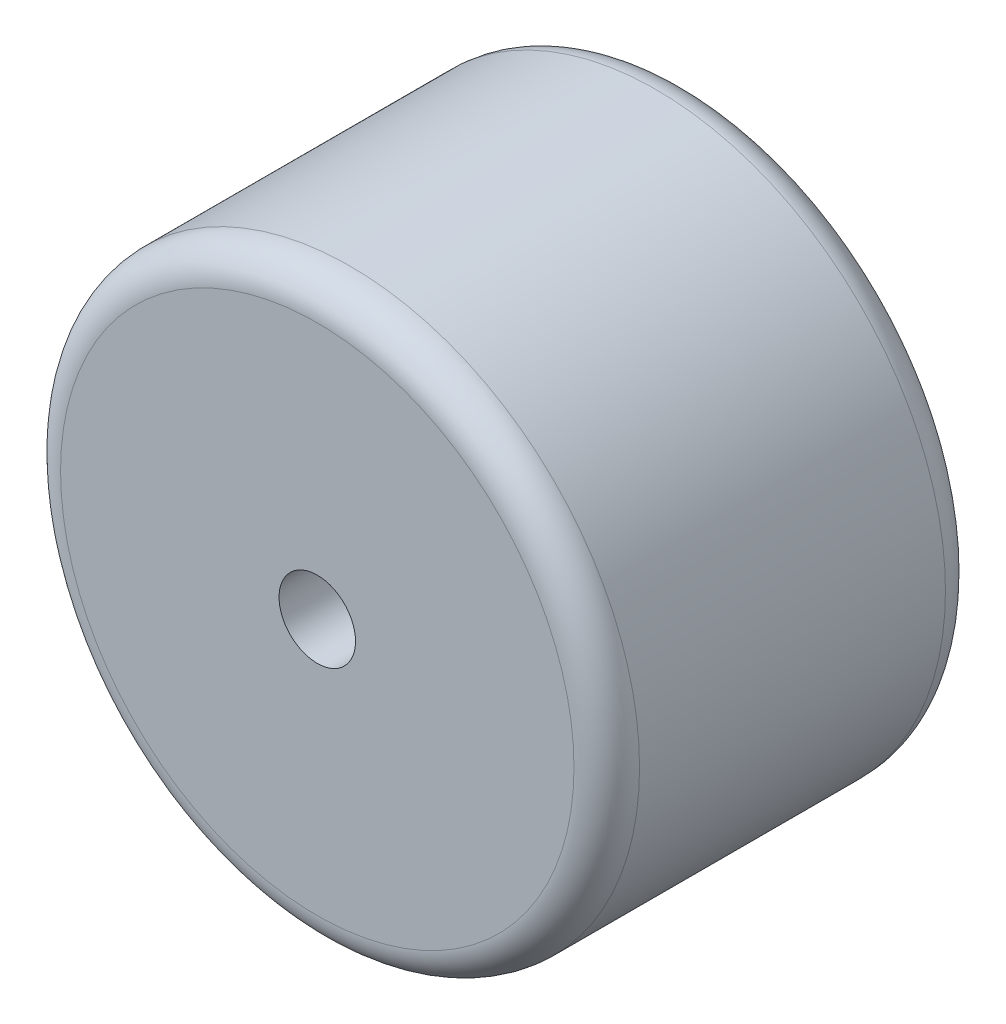
SolidWorks part; units mm, degrees
ref_plane "Front Plane" through (0, 0, 0) normal (0, 0, 1) x (1, 0, 0)
ref_plane "Top Plane" through (0, 0, 0) normal (0, 1, 0) x (1, 0, 0)
ref_plane "Right Plane" through (0, 0, 0) normal (1, 0, 0) x (0, 0, -1)
sketch "Sketch1" plane through (0, 0, 0) normal (0, 0, 1) x (1, 0, 0)
  circle A0 centre (0, 0) radius 26.5
  dimension "D1" = 53
extrude "Boss-Extrude1" add sketch "Sketch1" along normal blind 34 contours A0
fillet "Fillet1" radius 3 2 edges at (26.5, 0, 0) (26.5, 0, 34)
sketch "Sketch2" plane through (0, 0, 34) normal (0, 0, 1) x (1, 0, 0)
  circle A0 centre (0, 0) radius 3.5
  dimension "D1" = 7
extrude "Cut-Extrude1" cut sketch "Sketch2" against normal up to next
